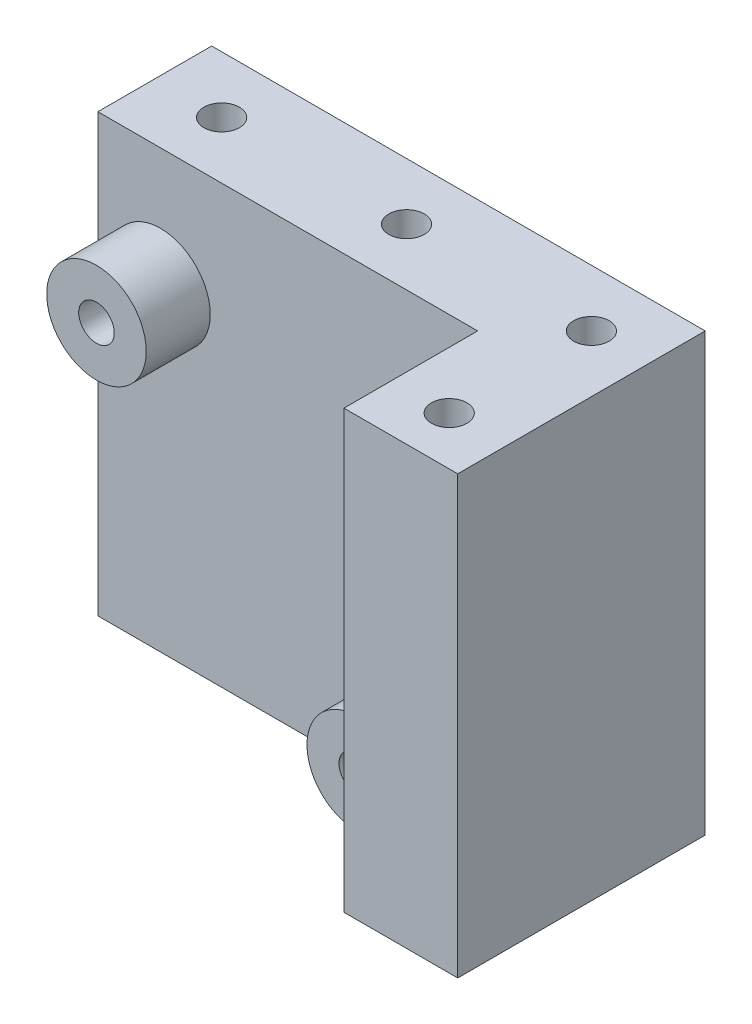
SolidWorks part; units mm, degrees
ref_plane "Plan de face" through (0, 0, 0) normal (0, 0, 1) x (1, 0, 0)
ref_plane "Plan de dessus" through (0, 0, 0) normal (0, 1, 0) x (1, 0, 0)
ref_plane "Plan de droite" through (0, 0, 0) normal (1, 0, 0) x (0, 0, -1)
sketch "Esquisse1" plane through (0, 0, 0) normal (0, 0, 1) x (1, 0, 0)
  line L1 (-34.7, 15.35) -> (0, 15.35)
  line L2 (-34.7, 15.35) -> (-34.7, -15.35)
  line L3 (-34.7, -15.35) -> (0, -15.35)
  line L4 (0, 15.35) -> (0, -15.35)
  point P4 (-17.35, 15.35)
  point P5 (0, 0)
  dimension "D1" = 30.7
  dimension "D2" = 34.7
extrude "Boss.-Extru.1" add sketch "Esquisse1" along normal blind 8
sketch "Esquisse2" plane through (0, 0, 8) normal (0, 0, 1) x (1, 0, 0)
  line L1 (0, 15.35) -> (-34.7, 15.35) construction
  line L2 (-34.7, -15.35) -> (0, -15.35) construction
  line L3 (0, -15.35) -> (0, 15.35) construction
  circle A0 centre (-30.3, 6.95) radius 3.5
  circle A1 centre (-12, -11.35) radius 3.5
  circle A2 centre (-30.3, 6.95) radius 1.25
  circle A3 centre (-12, -11.35) radius 1.25
  dimension "D3" = 7
  dimension "D4" = 30.3
  dimension "D6" = 2.5
  dimension "D7" = 2.5
  dimension "D2" = 8.4
  dimension "D5" = 4
  dimension "D8" = 12
extrude "Boss.-Extru.2" add sketch "Esquisse2" along normal mid plane 9
sketch "Esquisse3" plane through (0, 0, 8) normal (0, 0, 1) x (1, 0, 0)
  line L0 (0, 15.35) -> (-34.7, 15.35) construction
  line L1 (-8, 15.35) -> (0, 15.35)
  line L2 (-8, 15.35) -> (-8, -15.35)
  line L3 (-8, -15.35) -> (0, -15.35)
  line L4 (0, 15.35) -> (0, -15.35)
  dimension "D1" = 8
extrude "Boss.-Extru.3" add sketch "Esquisse3" along normal blind 9.4
sketch "Esquisse4" plane through (0, 15.35, 0) normal (0, 1, 0) x (1, 0, 0)
  line L0 (0, 0) -> (-34.7, 0) construction
  line L3 (0, -17.4) -> (0, 0) construction
  circle A0 centre (-4, -14) radius 1.25
  circle A1 centre (-4, -4) radius 1.25
  circle A2 centre (-17, -4) radius 1.25
  circle A3 centre (-30, -4) radius 1.25
  dimension "D1" = 14
  dimension "D2" = 2.5
  dimension "D3" = 4
  dimension "D4" = 13
  dimension "D5" = 26
  dimension "D6" = 4
extrude "Enlèv. mat.-Extru.1" cut sketch "Esquisse4" against normal through all
sketch "Esquisse6" plane through (0, 0, 8) normal (0, 0, 1) x (1, 0, 0)
  circle A0 centre (-30.3, 6.95) radius 1.25
  circle A1 centre (-30.3, 6.95) radius 1.25 construction
  circle A2 centre (-12, -11.35) radius 1.25
  circle A3 centre (-12, -11.35) radius 1.25 construction
extrude "Enlèv. mat.-Extru.2" cut sketch "Esquisse6" against normal through all
